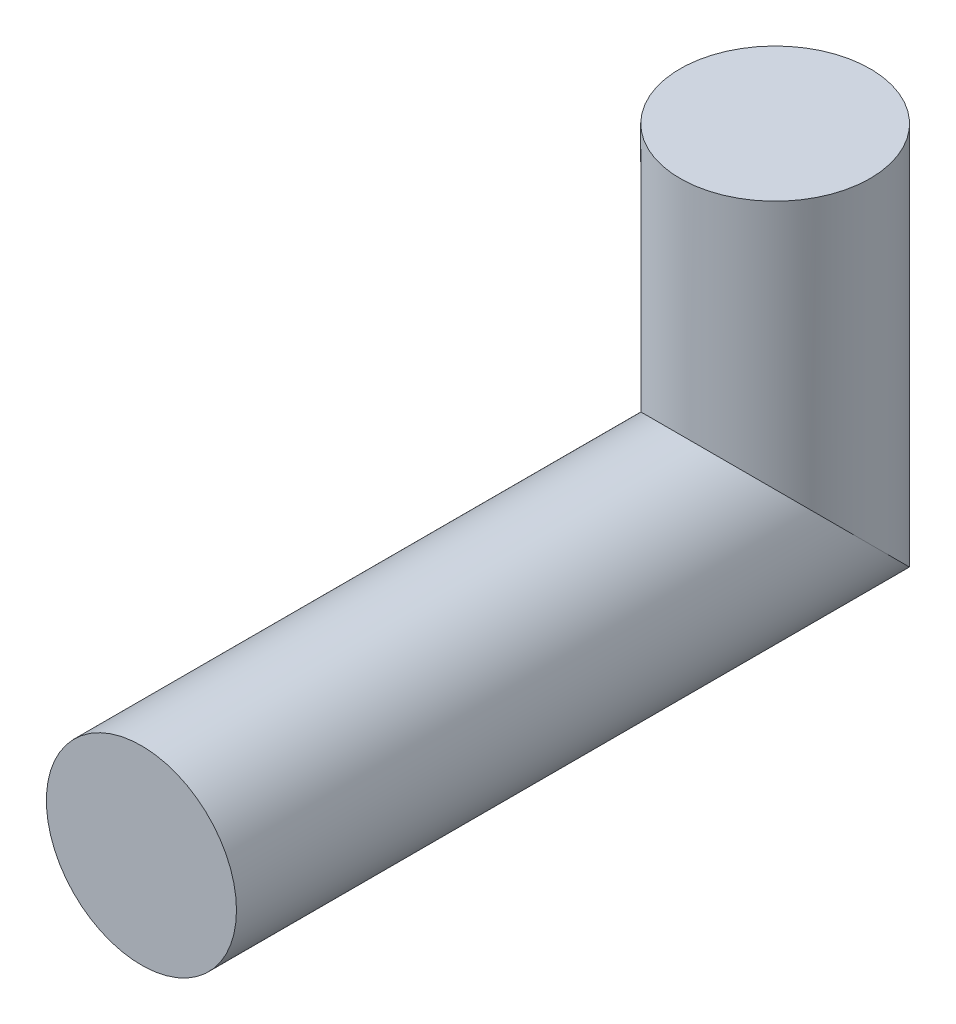
SolidWorks part; units mm, degrees
ref_plane "Front Plane" through (0, 0, 0) normal (0, 0, 1) x (1, 0, 0)
ref_plane "Top Plane" through (0, 0, 0) normal (0, 1, 0) x (1, 0, 0)
ref_plane "Right Plane" through (0, 0, 0) normal (1, 0, 0) x (0, 0, -1)
sketch "Sketch1" plane through (0, 0, 0) normal (0, 0, 1) x (1, 0, 0)
  circle A0 centre (0, 0) radius 19.05
  dimension "D1" = 38.1
sketch "Sketch2" plane through (0, 0, 0) normal (1, 0, 0) x (0, 0, -1)
  line L0 (0, 0) -> (127, 0)
  line L1 (127, 0) -> (127, 63.5)
  dimension "D1" = 63.5
  dimension "D2" = 127
sweep "Sweep1" add profiles "Sketch1" path "Sketch2"
